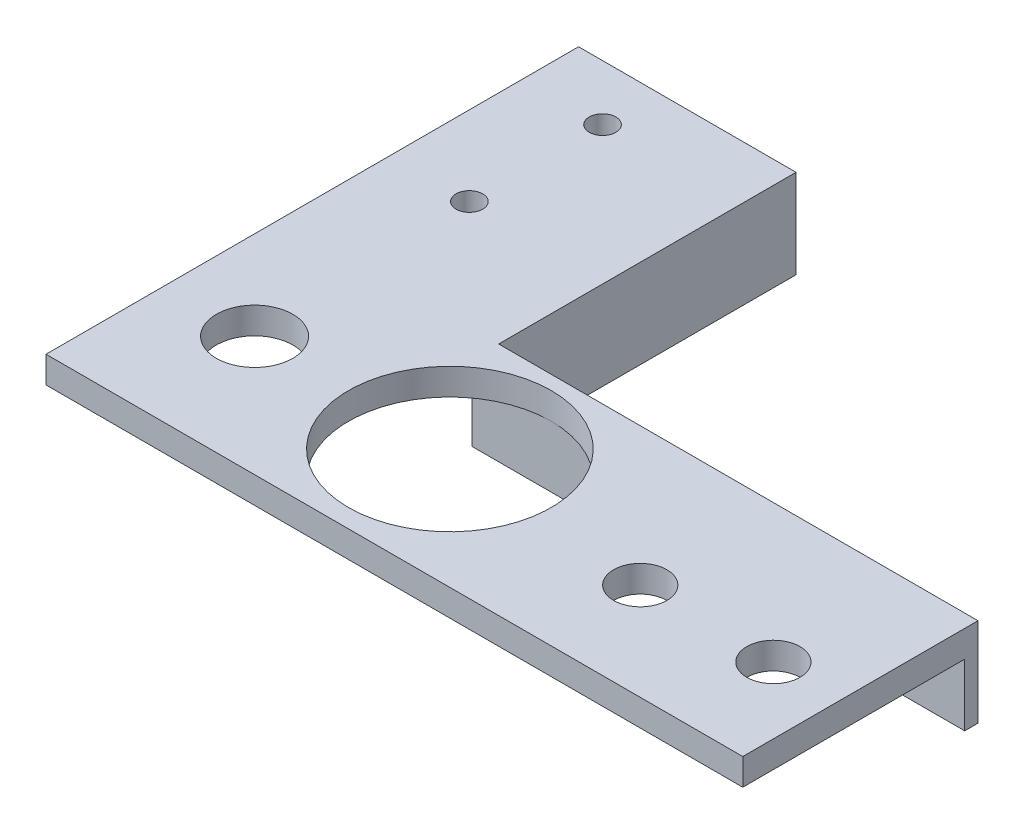
SolidWorks part; units mm, degrees
ref_plane "Alzado" through (0, 0, 0) normal (0, 0, 1) x (1, 0, 0)
ref_plane "Planta" through (0, 0, 0) normal (0, 1, 0) x (1, 0, 0)
ref_plane "Vista lateral" through (0, 0, 0) normal (1, 0, 0) x (0, 0, -1)
sketch "Croquis1" plane through (0, 0, 0) normal (0, 1, 0) x (1, 0, 0)
  line L0 (-16.25, 29) -> (-16.25, -6)
  line L1 (-39.25, -29) -> (39.25, -29) construction
  line L2 (-39.25, -29) -> (-39.25, 29) construction
  line L3 (-39.25, 29) -> (39.25, 29) construction
  line L4 (39.25, -29) -> (39.25, 29) construction
  line L5 (-39.25, -29) -> (39.25, 29) construction
  line L6 (-39.25, 29) -> (39.25, -29) construction
  line L7 (-16.25, -6) -> (39.25, -6)
  line L8 (-16.25, 29) -> (-39.25, 29)
  line L9 (-39.25, 29) -> (-39.25, -29)
  line L10 (-39.25, -29) -> (39.25, -29)
  line L11 (39.25, -29) -> (39.25, -6)
  point P0 (0, 0)
  dimension "D1" = 58
  dimension "D2" = 78.5
  dimension "D3" = 35
  dimension "D4" = 55.5
extrude "Saliente-Extruir1" add sketch "Croquis1" along normal blind 3
sketch "Croquis2" plane through (0, 3, 0) normal (0, 1, 0) x (1, 0, 0)
  line L0 (-39.25, -29) -> (39.25, -29) construction
  line L1 (39.25, -29) -> (39.25, -6) construction
  line L2 (-16.25, 29) -> (-39.25, 29) construction
  line L3 (-39.25, 29) -> (-39.25, -29) construction
  circle A0 centre (31.75, -20.05) radius 3
  circle A1 centre (16.75, -20.05) radius 3
  circle A2 centre (-30.3, 22.75) radius 1.5
  circle A3 centre (-30.3, 7.75) radius 1.5
  dimension "D4" = 6
  dimension "D6" = 6.25
  dimension "D7" = 8.95
  dimension "D8" = 3
  dimension "D1" = 8.95
  dimension "D2" = 15
  dimension "D3" = 7.5
  dimension "D5" = 15
extrude "Cortar-Extruir2" cut sketch "Croquis2" against normal through all
sketch "Croquis3" plane through (0, 3, 0) normal (0, 1, 0) x (1, 0, 0)
  line L0 (-16.25, 29) -> (-16.25, -6)
  line L1 (-16.25, -6) -> (39.25, -6)
  line L2 (39.25, -6) -> (39.25, -4.5)
  line L3 (39.25, -4.5) -> (-14.75, -4.5)
  line L4 (-14.75, -4.5) -> (-14.75, 29)
  line L5 (-14.75, 29) -> (-16.25, 29)
  dimension "D1" = 1.5
extrude "Saliente-Extruir2" add sketch "Croquis3" against normal blind 10
sketch "Croquis4" plane through (0, 3, 0) normal (0, 1, 0) x (1, 0, 0)
  circle A0 centre (-7.25, -17.5) radius 11.4206
extrude "Cortar-Extruir3" cut sketch "Croquis4" against normal through all
sketch "Croquis5" plane through (0, 0, 29) normal (0, 0, 1) x (1, 0, 0)
  line L1 (-39.25, 0) -> (39.25, 0)
  line L2 (-39.25, 0) -> (-39.25, 3)
  line L3 (-39.25, 3) -> (39.25, 3)
  line L4 (39.25, 0) -> (39.25, 3)
extrude "Saliente-Extruir3" add sketch "Croquis5" along normal blind 2
sketch "Croquis6" plane through (0, 3, 0) normal (0, 1, 0) x (1, 0, 0)
  circle A0 centre (-29.25, -17.5) radius 4.3047
extrude "Cortar-Extruir4" cut sketch "Croquis6" against normal through all
